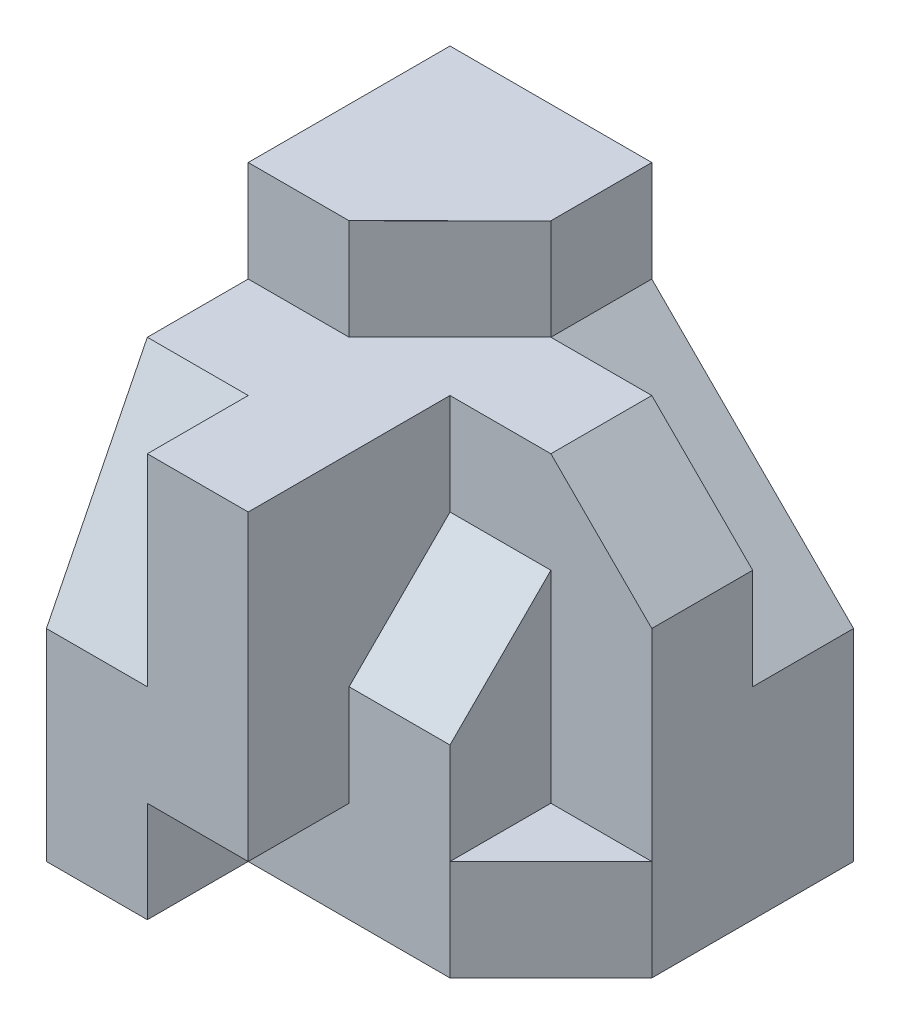
SolidWorks part; units mm, degrees
ref_plane "Front Plane" through (0, 0, 0) normal (0, 0, 1) x (1, 0, 0)
ref_plane "Top Plane" through (0, 0, 0) normal (0, 1, 0) x (1, 0, 0)
ref_plane "Right Plane" through (0, 0, 0) normal (1, 0, 0) x (0, 0, -1)
sketch "Sketch1" plane through (0, 0, 0) normal (0, 0, 1) x (1, 0, 0)
  line L1 (2, -2.5) -> (-2, -2.5)
  line L2 (2, -2.5) -> (2, 2.5)
  line L3 (2, 2.5) -> (-2, 2.5)
  line L4 (-2, -2.5) -> (-2, 2.5)
  line L5 (2, -2.5) -> (-2, 2.5) construction
  line L6 (2, 2.5) -> (-2, -2.5) construction
  point P0 (0, 0)
  dimension "D1" = 5
  dimension "D2" = 4
extrude "Boss-Extrude1" add sketch "Sketch1" along normal blind 4
sketch "Sketch2" plane through (0, 2.5, 0) normal (0, 1, 0) x (1, 0, 0)
  line L0 (0, 0) -> (0, -1)
  line L1 (2, 0) -> (-2, 0) construction
  line L2 (0, -1) -> (-1, -2)
  line L3 (-1, -2) -> (-2, -2)
  line L4 (-2, -4) -> (-2, 0) construction
  line L5 (-2, -2) -> (-2, 0)
  line L6 (-2, 0) -> (0, 0)
  dimension "D1" = 1
  dimension "D2" = 1
  dimension "D3" = 2
  dimension "D4" = 2
extrude "Cut-Extrude1" cut sketch "Sketch2" against normal blind 1 flip side to cut
sketch "Sketch3" plane through (0, 0, 0) normal (0, 0, -1) x (-1, 0, 0)
  line L0 (0, 1.5) -> (-2, -0.5)
  line L1 (-2, -2.5) -> (-2, 1.5) construction
  line L2 (-2, -0.5) -> (-2, 1.5)
  line L3 (-2, 1.5) -> (0, 1.5)
  dimension "D1" = 2
extrude "Cut-Extrude2" cut sketch "Sketch3" against normal blind 1
sketch "Sketch4" plane through (-2, 0, 0) normal (-1, 0, 0) x (0, 0, 1)
  line L0 (3, 1.5) -> (4, -0.5)
  line L1 (2, 1.5) -> (4, 1.5) construction
  line L2 (4, 1.5) -> (4, -2.5) construction
  line L3 (4, -0.5) -> (4, 1.5)
  line L4 (4, 1.5) -> (3, 1.5)
  dimension "D1" = 1
  dimension "D2" = 2
extrude "Cut-Extrude3" cut sketch "Sketch4" against normal blind 1
sketch "Sketch5" plane through (0, 0, 4) normal (0, 0, 1) x (1, 0, 0)
  line L0 (2, 1.5) -> (1, 1.5)
  line L1 (2, 1.5) -> (-1, 1.5) construction
  line L2 (1, 1.5) -> (2, 0.5)
  line L3 (2, -2.5) -> (2, 1.5) construction
  line L4 (2, 0.5) -> (2, 1.5)
  dimension "D1" = 1
  dimension "D2" = 1
extrude "Cut-Extrude4" cut sketch "Sketch5" against normal through all
sketch "Sketch6" plane through (0, 0, 4) normal (0, 0, 1) x (1, 0, 0)
  line L0 (-1, -2.5) -> (-1, -1.5)
  line L1 (-2, -2.5) -> (2, -2.5) construction
  line L2 (-1, -1.5) -> (0, -1.5)
  line L3 (0, -1.5) -> (0, 1.5)
  line L4 (-1, 1.5) -> (0, 1.5) construction
  line L5 (0, 1.5) -> (1, 1.5)
  line L6 (1, 1.5) -> (2, 0.5)
  line L7 (2, 0.5) -> (2, -2.5)
  line L8 (2, -2.5) -> (-1, -2.5)
  dimension "D1" = 1
  dimension "D2" = 1
  dimension "D3" = 3
extrude "Cut-Extrude5" cut sketch "Sketch6" against normal blind 1
sketch "Sketch7" plane through (0, 1.5, 0) normal (0, 1, 0) x (1, 0, 0)
  line L0 (0, -2) -> (2, -2)
  line L1 (2, -2) -> (2, -3)
  line L2 (2, -3) -> (0, -3)
  line L3 (0, -3) -> (0, -2)
  line L4 (2, -1) -> (2, -3) construction
  line L5 (0, -3) -> (0, -4) construction
  line L6 (1, -3) -> (0, -3) construction
  dimension "D1" = 1
extrude "Cut-Extrude6" cut sketch "Sketch7" against normal blind 1
sketch "Sketch8" plane through (2, 0, 0) normal (1, 0, 0) x (0, 0, -1)
  line L0 (-2, 0.5) -> (-3, -0.5)
  line L1 (-3, 0.5) -> (-3, -1.5) construction
  line L2 (-3, -0.5) -> (-3, 0.5)
  line L3 (-3, 0.5) -> (-2, 0.5)
  dimension "D1" = 2
extrude "Cut-Extrude7" cut sketch "Sketch8" against normal blind 2
sketch "Sketch9" plane through (0, 1.5, 0) normal (0, 1, 0) x (1, 0, 0)
  line L0 (2, -2) -> (1, -2)
  line L1 (1, -2) -> (1, -3)
  line L2 (0, -3) -> (2, -3) construction
  line L3 (1, -3) -> (2, -3)
  line L4 (2, -3) -> (2, -2)
  dimension "D1" = 1
extrude "Cut-Extrude9" cut sketch "Sketch9" against normal blind 3
sketch "Sketch10" plane through (0, -1.5, 0) normal (0, 1, 0) x (1, 0, 0)
  line L0 (2, -2) -> (1, -3)
  line L1 (1, -3) -> (2, -3)
  line L2 (2, -3) -> (2, -2)
extrude "Cut-Extrude10" cut sketch "Sketch10" against normal blind 3
